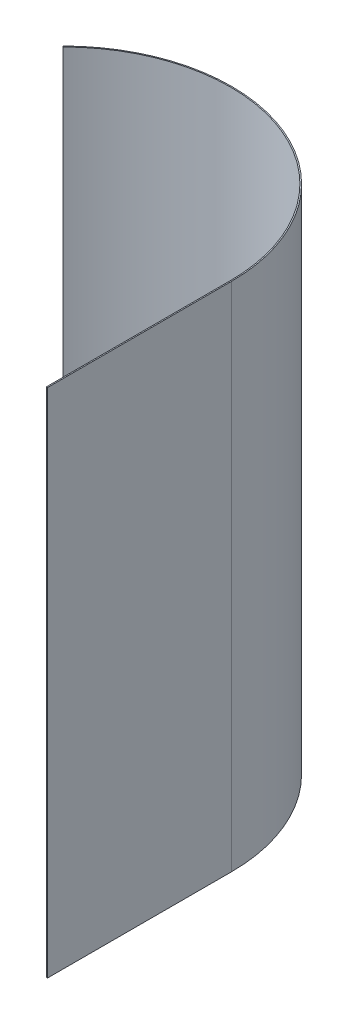
SolidWorks part; units mm, degrees
material "Acero Galvanizado"
ref_plane "Alzado" through (0, 0, 0) normal (0, 0, 1) x (1, 0, 0)
ref_plane "Planta" through (0, 0, 0) normal (0, 1, 0) x (1, 0, 0)
ref_plane "Vista lateral" through (0, 0, 0) normal (1, 0, 0) x (0, 0, -1)
sketch "Croquis3" plane through (0, 0, 0) normal (0, 1, 0) x (1, 0, 0)
  line L0 (31.15, 127.7418) -> (31.15, -52.2582)
  line L1 (-250.5226, 244.4144) -> (-133.85, 127.7418) construction
  line L2 (-133.85, 127.7418) -> (31.15, 127.7418) construction
  line L3 (-31.15, 52.2582) -> (-31.15, -127.7418) construction
  line L4 (250.5226, -244.4144) -> (133.85, -127.7418) construction
  line L5 (133.85, -127.7418) -> (-31.15, -127.7418) construction
  line L6 (31.15, -52.2582) -> (30, -52.2582)
  line L7 (30, -52.2582) -> (30, 127.7418)
  line L8 (-249.7094, 243.6013) -> (-250.5226, 244.4144)
  line L9 (375, 0) -> (31.15, 0) construction
  line L10 (4.7861, -52.2582) -> (4.7861, 0) construction
  line L11 (4.7861, 0) -> (4.7861, 52.2582) construction
  line L12 (0, 0) -> (30, 0) construction
  circle A0 centre (0, 0) radius 350 construction
  arc A1 (-250.5226, 244.4144) -> (31.15, 127.7418) centre (-133.85, 127.7418) cw
  arc A2 (-31.15, -127.7418) -> (250.5226, -244.4144) centre (133.85, -127.7418) ccw construction
  arc A3 (30, 127.7418) -> (-249.7094, 243.6013) centre (-133.85, 127.7418) ccw
  circle A4 centre (0, 0) radius 19.05 construction
  circle A5 centre (0, 0) radius 375 construction
  dimension "D1" = 700
  dimension "D4" = 31.15
  dimension "D3" = 165
  dimension "D6" = 165
  dimension "D13" = 38.1
  dimension "D14" = 750
  dimension "D15" = 52.2582
  dimension "D2" = 135
  dimension "D5" = 31.15
  dimension "D7" = 135
  dimension "D8" = 90
  dimension "D9" = 90
  dimension "D10" = 180
  dimension "D11" = 180
  dimension "D12" = 1.15
  dimension "D16" = 52.2582
  dimension "D17" = 104.5164
extrude "Saliente-Extruir1" add sketch "Croquis3" along normal blind 500
